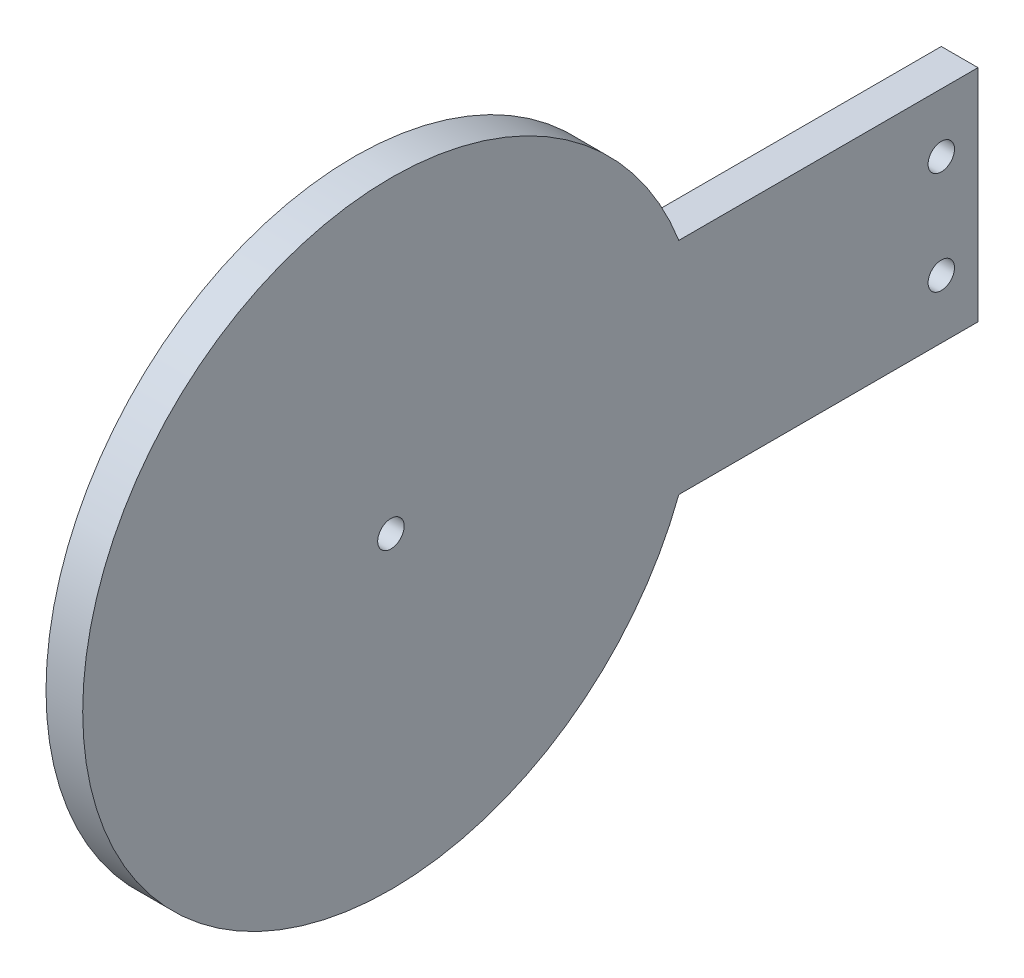
SolidWorks part; units mm, degrees
ref_plane "정면" through (0, 0, 0) normal (0, 0, 1) x (1, 0, 0)
ref_plane "윗면" through (0, 0, 0) normal (0, 1, 0) x (1, 0, 0)
ref_plane "우측면" through (0, 0, 0) normal (1, 0, 0) x (0, 0, -1)
ref_plane "평면1" through (-9, 0, 0) normal (-1, 0, 0) x (0, -1, 0)
sketch "스케치1" plane through (-9, 0, 0) normal (-1, 0, 0) x (0, -1, 0)
  line L0 (-21, -18.1229) -> (-21, 2.2621)
  line L1 (-6, -18.1229) -> (-6, 2.2621)
  line L3 (-13.5, 21.8771) -> (7.5, 21.8771) construction
  line L4 (7.5, 21.8771) -> (-34.5, 21.8771) construction
  line L5 (-13.5, 21.8771) -> (-13.5, -66.3671) construction
  line L8 (-21, -18.1229) -> (-6, -18.1229)
  circle A1 centre (-13.5, 21.8771) radius 21 construction
  circle A2 centre (-13.5, 21.8771) radius 30 construction
  arc A3 (-6, 2.2621) -> (-21, 2.2621) centre (-13.5, 21.8771) ccw
  point P12 (7.5, 0.4528)
  point P17 (-34.5, 0.4528)
  dimension "D2" = 40
extrude "보스-돌출1" add sketch "스케치1" against normal blind 2.5
ref_plane "평면2" through (0, 13.5, 0) normal (0, 1, 0) x (1, 0, 0)
sketch "스케치2" plane through (-6.5, 0, 0) normal (1, 0, 0) x (0, 0, -1)
  line L0 (18.1229, 21) -> (18.1229, 6) construction
  line L1 (18.1229, 6) -> (-2.2621, 6) construction
  line L2 (-2.2621, 21) -> (18.1229, 21) construction
  circle A0 centre (15.6229, 10) radius 0.9
  circle A1 centre (15.6229, 17) radius 0.9
  circle A2 centre (-21.8771, 13.5) radius 0.9
  dimension "D1" = 1.8
  dimension "D2" = 1.8
  dimension "D7" = 1.8
  dimension "D3" = 2.5
  dimension "D4" = 2.5
  dimension "D5" = 4
  dimension "D6" = 4
extrude "컷-돌출1" cut sketch "스케치2" against normal through all
